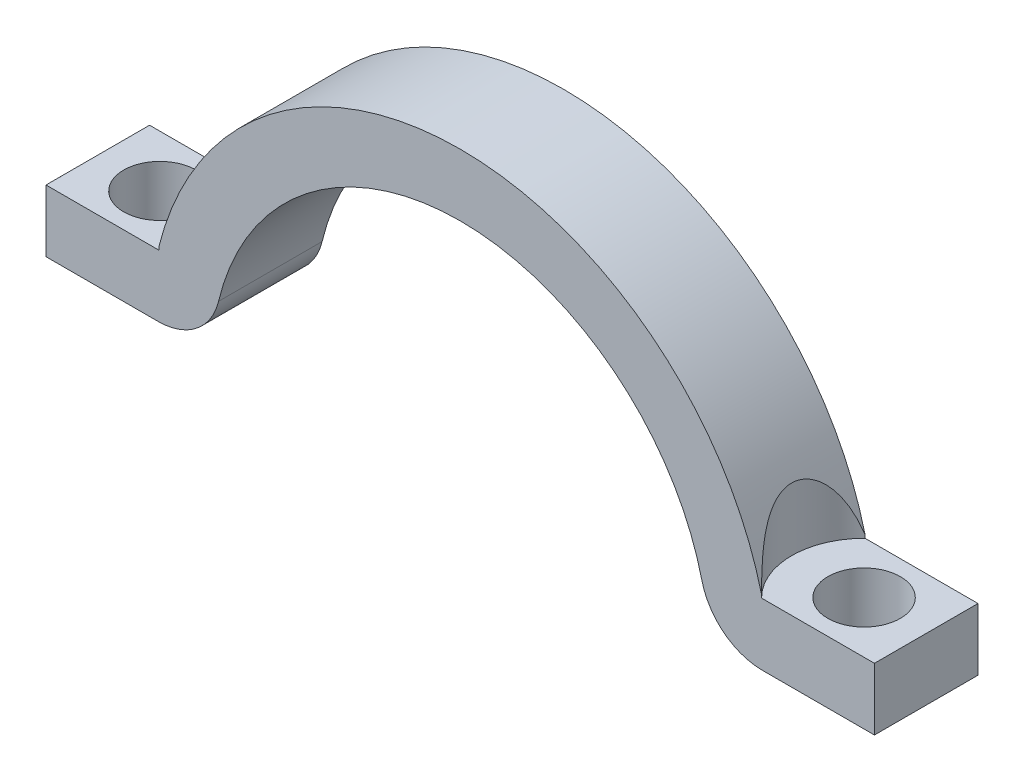
SolidWorks part; units mm, degrees
ref_plane "Plan de face" through (0, 0, 0) normal (0, 0, 1) x (1, 0, 0)
ref_plane "Plan de dessus" through (0, 0, 0) normal (0, 1, 0) x (1, 0, 0)
ref_plane "Plan de droite" through (0, 0, 0) normal (1, 0, 0) x (0, 0, -1)
sketch "Esquisse1" plane through (0, 0, 0) normal (0, 0, 1) x (1, 0, 0)
  line L0 (-14.2536, 0) -> (18.373, 0) construction
  line L1 (-20, 0.5) -> (-14.586, 0.5)
  line L2 (-20, 0.5) -> (-20, 3.5)
  line L3 (-20, 3.5) -> (-14.586, 3.5)
  line L4 (20, 0.5) -> (20, 3.5)
  line L5 (20, 3.5) -> (14.586, 3.5)
  line L6 (14.586, 0.5) -> (20, 0.5)
  arc A0 (14.586, 3.5) -> (-14.586, 3.5) centre (0, 0) ccw
  arc A1 (11.6688, 2.8) -> (-11.6688, 2.8) centre (0, 0) ccw
  arc A2 (14.586, 0.5) -> (11.6688, 2.8) centre (14.586, 3.5) cw
  arc A3 (-11.6688, 2.8) -> (-14.586, 0.5) centre (-14.586, 3.5) cw
  point P11 (0, 0)
  point P13 (0, 0)
  dimension "D1" = 24
  dimension "D2" = 3
  dimension "D7" = 3
  dimension "D3" = 1
  dimension "D4" = 3
  dimension "D5" = 40
  dimension "D6" = 20
extrude "Boss.-Extru.2" add sketch "Esquisse1" along normal blind 5
sketch "Esquisse3" plane through (0, 3.5, 0) normal (0, 1, 0) x (1, 0, 0)
  line L0 (-20, -5) -> (-20, 0) construction
  circle A0 centre (-17, -2.5) radius 1.75
  circle A1 centre (17, -2.5) radius 1.75
  point P6 (-20, -2.5)
  dimension "D1" = 3.5
  dimension "D2" = 34
  dimension "D3" = 17
extrude "Enlèv. mat.-Extru.2" cut sketch "Esquisse3" against normal through all
sketch "Esquisse4" plane through (0, 3.5, 0) normal (0, 1, 0) x (1, 0, 0)
  circle A0 centre (-17, -2.5) radius 3.5
  circle A1 centre (17, -2.5) radius 3.5
  dimension "D1" = 7
  dimension "D2" = 7
extrude "Enlèv. mat.-Extru.3" cut sketch "Esquisse4" along normal through all
